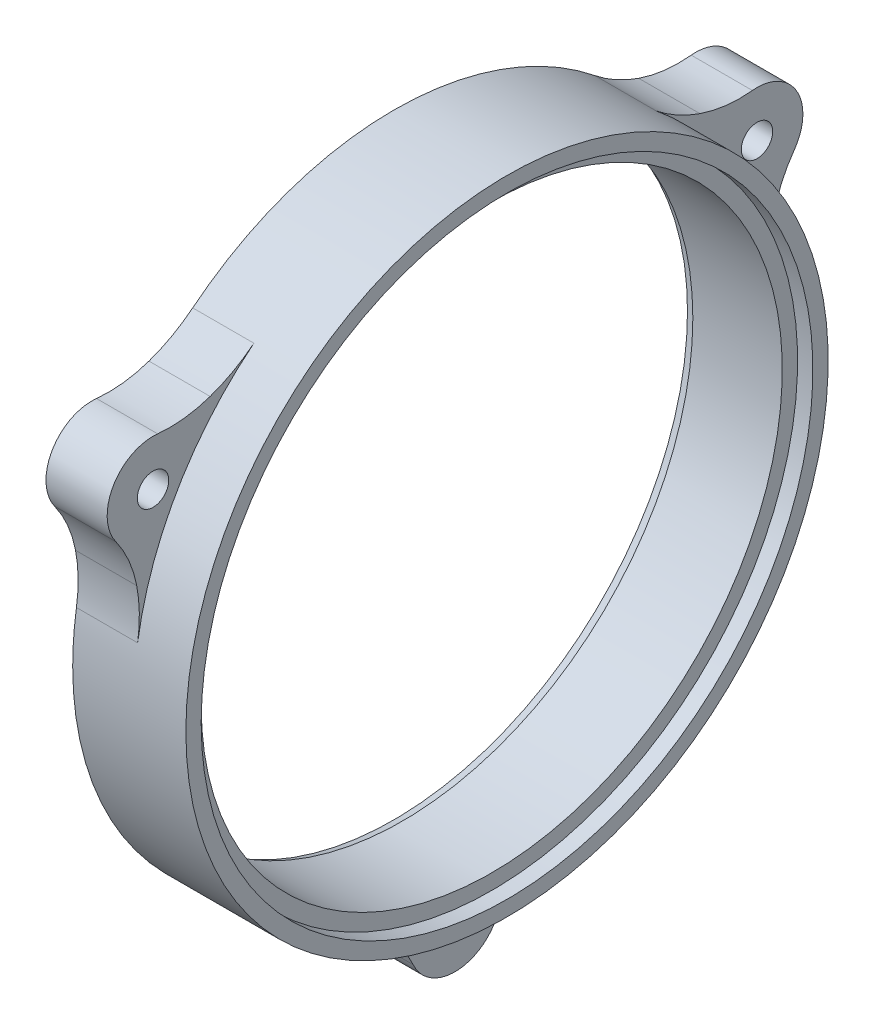
SolidWorks part; units mm, degrees
material "6061-T6 (SS)"
ref_plane "Front Plane" through (0, 0, 0) normal (0, 0, 1) x (1, 0, 0)
ref_plane "Top Plane" through (0, 0, 0) normal (0, 1, 0) x (1, 0, 0)
ref_plane "Right Plane" through (0, 0, 0) normal (1, 0, 0) x (0, 0, -1)
sketch "Sketch1" plane through (0, 0, 0) normal (0, 0, 1) x (1, 0, 0)
  line L0 (0, 0) -> (50000, 0) construction
  line L2 (0, 66.675) -> (23.495, 66.675)
  line L3 (23.495, 66.675) -> (23.495, 63.5)
  line L4 (23.495, 63.5) -> (20.32, 63.5)
  line L5 (20.32, 63.5) -> (20.32, 60.325)
  line L6 (20.32, 60.325) -> (0, 60.325)
  line L7 (0, 60.325) -> (0, 66.675)
  dimension "D1" = 20.32
  dimension "D2" = 3.175
  dimension "D3" = 3.175
  dimension "D4" = 60.325
  dimension "D5" = 3.175
revolve "Revolve1" add sketch "Sketch1" angle 360 about L0
sketch "Sketch5" plane through (0, 0, 0) normal (-1, 0, 0) x (0, 0, 1)
  line L0 (8.5292, -4.9243) -> (-26667.7241, 15396.6177) construction
  line L1 (0, 0) -> (0, 50000) construction
  arc A0 (-61.7336, 45.6717) -> (-70.4197, 30.6271) centre (-62.6916, 36.195) ccw
  arc A2 (-66.0808, 20.5541) -> (-65.8943, 10.1735) centre (-96.0174, 14.8242) cw
  circle A3 centre (0, 0) radius 66.675 construction
  arc A4 (-50.8408, 46.9506) -> (-41.7576, 51.9794) centre (-60.8468, 75.7414) ccw
  arc A5 (-66.0808, 20.5541) -> (-70.4197, 30.6271) centre (-91.028, 15.7792) ccw
  arc A6 (-50.8408, 46.9506) -> (-61.7336, 45.6717) centre (-59.1791, 70.9429) cw
  arc A7 (-65.8943, 10.1735) -> (-41.7576, 51.9794) centre (0, 0) cw
  point P14 (-33.7808, 36.195)
  dimension "D1" = 30.48
  dimension "D2" = 25.4
  dimension "D3" = 9.525
  dimension "D4" = 72.39
  dimension "D5" = 30.48
  dimension "D6" = 60
extrude "Boss-Extrude1" add sketch "Sketch5" against normal blind 12.7
hole_wizard "1/4 Clearance Hole1" positions "Sketch7" profile "Sketch6" hole size "1/4" standard "Ansi Inch" end condition through all
sketch "Sketch7" plane through (0, 0, 0) normal (-1, 0, 0) x (0, 0, 1)
  arc A0 (-61.7336, 45.6717) -> (-70.4197, 30.6271) centre (-62.6916, 36.195) ccw construction
  point P0 (-62.6916, 36.195)
sketch "Sketch6" plane through (0, 36.195, -62.6916) normal (0, 1, 0) x (0, 0, 1)
  line L0 (0, 0) -> (0, 23.495)
  line L1 (0, 23.495) -> (3.2639, 23.495)
  line L2 (3.2639, 23.495) -> (3.2639, 0)
  line L5 (3.2639, 0) -> (0, 0)
  line L11 (0, -6.35) -> (0, 107.95) construction
  dimension "Thru Hole Dia." = 6.5278
  dimension "Thru Hole Depth" = 23.495
pattern_circular "CirPattern1" count 3 over 360 about axis through (0, 0, 0) along (1, 0, 0) of "Boss-Extrude1", "1/4 Clearance Hole1"
chamfer "Chamfer1" distance 0.635 angle 70 1 edges at (0, 0, 60.325)
